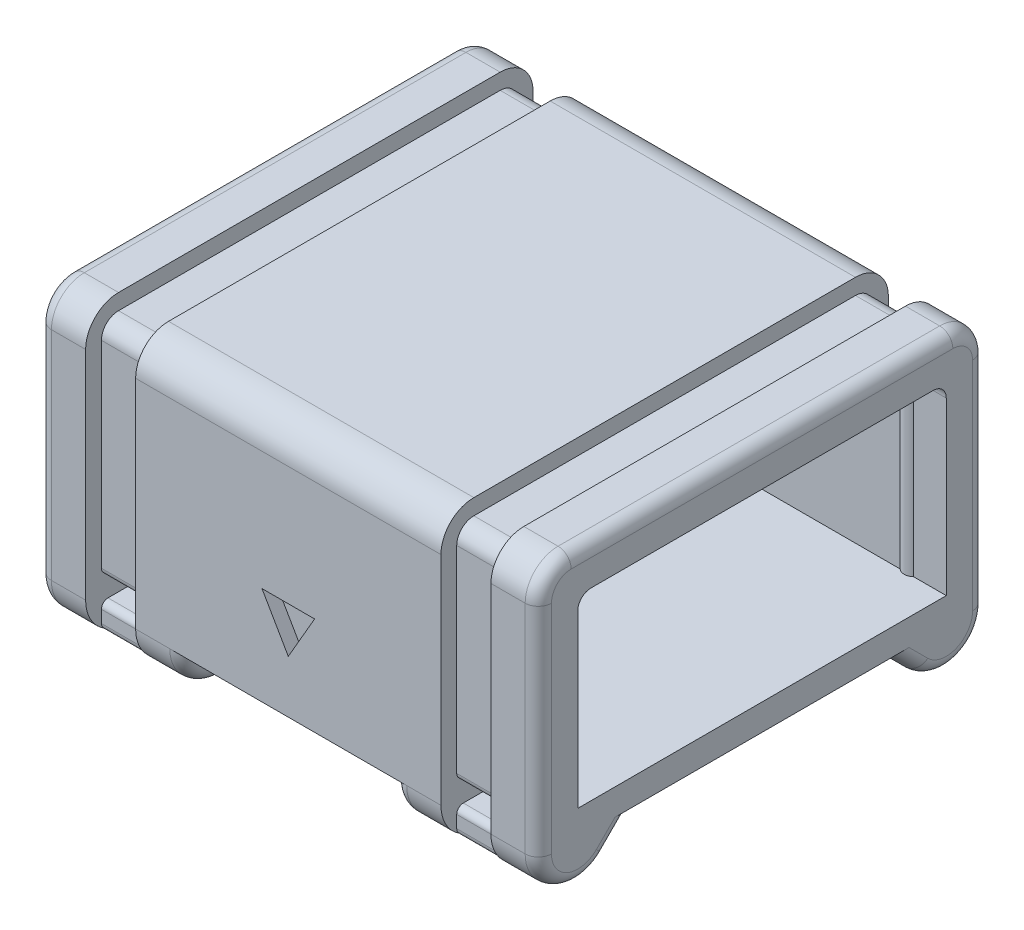
SolidWorks part; units mm, degrees
ref_plane "Ebene vorne" through (0, 0, 0) normal (0, 0, 1) x (1, 0, 0)
ref_plane "Ebene oben" through (0, 0, 0) normal (0, 1, 0) x (1, 0, 0)
ref_plane "Ebene rechts" through (0, 0, 0) normal (1, 0, 0) x (0, 0, -1)
ref_plane "Ebene1" through (13.5, 0, 0) normal (1, 0, 0) x (0, 0, -1)
ref_plane "Ebene2" through (-13.5, 0, 0) normal (1, 0, 0) x (0, 0, -1)
sketch "Skizze2" plane through (0, 0, 0) normal (1, 0, 0) x (0, 0, -1)
  line L0 (-14, 9) -> (14, 9)
  line L4 (-17, 14.5) -> (-17, 0)
  line L5 (14.5, 17) -> (-14.5, 17)
  line L6 (17, 14.5) -> (17, 0)
  line L7 (14, 9) -> (14, 0)
  line L8 (17, 0) -> (14, 0)
  line L9 (-14, 9) -> (-14, 0)
  line L10 (-14, 0) -> (-17, 0)
  line L11 (0, 0) -> (0, 4.6223) construction
  arc A2 (-14.5, 17) -> (-17, 14.5) centre (-14.5, 14.5) ccw
  arc A3 (17, 14.5) -> (14.5, 17) centre (14.5, 14.5) ccw
  dimension "D5" = 3
  dimension "D6" = 34
  dimension "D2" = 2.5
  dimension "D1" = 17
  dimension "D3" = 9
  dimension "D7" = 3
extrude "Aufsatz-Linear austragen2" add sketch "Skizze2" along normal mid plane 38
sketch "Skizze5" plane through (0, 0, -17) normal (0, 0, 1) x (1, 0, 0)
  line L0 (0, 2) -> (-2, 5.4641)
  line L1 (-2, 5.4641) -> (2, 5.4641)
  line L2 (2, 5.4641) -> (0, 2)
  line L3 (0, 5.4641) -> (0, 2) construction
  dimension "D1" = 4
  dimension "D2" = 2
sketch "Skizze9" plane through (0, 0, 17) normal (0, 0, -1) x (-1, 0, 0)
  line L0 (0, 2) -> (-2, 5.4641)
  line L1 (-2, 5.4641) -> (2, 5.4641)
  line L2 (2, 5.4641) -> (0, 2)
  line L3 (0, 5.4641) -> (0, 2) construction
  dimension "D1" = 4
sketch "Skizze8" plane through (0, 0, 0) normal (1, 0, 0) x (0, 0, -1)
  line L0 (14.5, 17) -> (-14.5, 17) construction
  line L17 (-14, 9) -> (14, 9)
  line L18 (14, 9) -> (14, 13)
  line L25 (13, 14) -> (-13, 14)
  line L28 (-14, 13) -> (-14, 9)
  arc A0 (-14, 13) -> (-13, 14) centre (-13, 13) cw
  arc A1 (13, 14) -> (14, 13) centre (13, 13) cw
  dimension "D2" = 1
  dimension "D1" = 3
extrude "Schnitt-Linear austragen3" cut sketch "Skizze8" against normal mid plane 34
sketch "Skizze17" plane through (-19, 0, 0) normal (-1, 0, 0) x (0, 0, 1)
  line L0 (-17, 0) -> (17, 0)
  line L1 (17, 0) -> (17, -2)
  line L2 (11.8787, -4.1213) -> (9.7574, -2)
  line L3 (9.7574, -2) -> (-9.7574, -2)
  line L4 (0, -1.2233) -> (0, -7.3474) construction
  line L5 (-11.8787, -4.1213) -> (-9.7574, -2)
  line L6 (-17, 0) -> (-17, -2)
  line L7 (-14, 0) -> (-17, 0) construction
  arc A0 (17, -2) -> (11.8787, -4.1213) centre (14, -2) cw
  arc A1 (-17, -2) -> (-11.8787, -4.1213) centre (-14, -2) ccw
  point P15 (0, -2)
  point P16 (0, 0)
  dimension "D3" = 3
  dimension "D1" = 2
  dimension "D4" = 90
  dimension "D5" = 5
extrude "Aufsatz-Linear austragen9" add sketch "Skizze17" against normal up to surface (38 mm away) up to face at (19, 8.2036, 0)
sketch "Skizze14" plane through (-19, 0, 0) normal (-1, 0, 0) x (0, 0, 1)
  line L0 (14, 0) -> (14, 9) construction
  line L1 (-14, 9) -> (14, 9)
  line L2 (-14, 9) -> (-14, 0)
  line L3 (-14, 0) -> (14, 0)
  line L4 (14, 9) -> (14, 0)
  line L5 (-14, 9) -> (-14, 0) construction
extrude "Aufsatz-Linear austragen8" add sketch "Skizze14" against normal up to surface (2 mm away) up to face at (-17, 12.069, 0)
sketch "Skizze12" plane through (19, 0, 0) normal (1, 0, 0) x (0, 0, -1)
  line L0 (-14, 9) -> (14, 9) construction
  line L1 (-14, 9) -> (14, 9)
  line L2 (-14, 9) -> (-14, 13)
  line L3 (-13, 14) -> (13, 14)
  line L4 (14, 9) -> (14, 13)
  line L5 (0, 14) -> (0, 5.9274) construction
  line L6 (-14, 0) -> (-14, 9) construction
  line L7 (14, 9) -> (14, 0) construction
  line L8 (-14, 0) -> (-14, 9) construction
  arc A0 (14, 13) -> (13, 14) centre (13, 13) ccw
  arc A1 (-13, 14) -> (-14, 13) centre (-13, 13) ccw
  dimension "D1" = 1
  dimension "D2" = 5
extrude "Schnitt-Linear austragen5" cut sketch "Skizze12" against normal up to surface (2 mm away) up to face at (17, 12.069, 0)
sketch "Skizze19" plane through (0, 14, 0) normal (0, 1, 0) x (1, 0, 0)
  line L0 (15.5, 14) -> (16.5, 14)
  line L3 (0, 0) -> (5.7188, 0) construction
  line L4 (15.5, -14) -> (16.5, -14)
  line L5 (-17, 14) -> (19, 14) construction
  line L6 (19, 14.5) -> (19, -14.5) construction
  arc A0 (15.5, 14) -> (16.5, 14) centre (16, 14.525) ccw
  arc A1 (15.5, -14) -> (16.5, -14) centre (16, -14.525) cw
  dimension "D1" = 1
  dimension "D2" = 2.5
  dimension "D3" = 0.2
extrude "Aufsatz-Linear austragen10" add sketch "Skizze19" against normal blind 14
sketch "Skizze20" plane through (-17, 0, 0) normal (1, 0, 0) x (0, 0, -1)
  circle A0 centre (0, 2) radius 1.5
extrude "Schnitt-Linear austragen7" cut sketch "Skizze20" against normal through all and the other way through all contours A0
pattern_linear "Lineares Muster1" count 2 spacing 24 along (-1, 0, 0) of "Aufsatz-Linear austragen10"
sketch "Skizze21" plane through (0, 0, 0) normal (0, 0, 1) x (1, 0, 0)
  line L0 (-8, -2) -> (8, -2)
  line L1 (8, -2) -> (8, -5)
  line L2 (8, -5) -> (-8, -5)
  line L3 (-8, -5) -> (-8, -2)
  line L4 (19, -2) -> (-19, -2) construction
  line L5 (0, 0) -> (0, -2) construction
  dimension "D1" = 16
  dimension "D2" = 3
extrude "Schnitt-Linear austragen9" cut sketch "Skizze21" against normal through all both and the other way through all
sketch "Skizze10" plane through (-19, -2, 0) normal (1, 0, 0) x (0, -1, 0)
  line L0 (-1.8688, 0) -> (-7, 0) construction
  line L1 (-7, -6.2274) -> (-7, 6.2274) construction
  line L3 (-17, -0.75) -> (-17, 0.75)
  line L4 (-17, -0.75) -> (-7, -0.75)
  line L5 (-7, -0.75) -> (-7, 0.75)
  line L6 (-17, 0.75) -> (-7, 0.75)
  line L7 (-14, -10.65) -> (-14, -9.15)
  line L8 (-14, -10.65) -> (-7, -10.65)
  line L9 (-7, -10.65) -> (-7, -9.15)
  line L10 (-14, -9.15) -> (-7, -9.15)
  line L11 (-14, -7.35) -> (-14, -5.85)
  line L12 (-14, -7.35) -> (-7, -7.35)
  line L13 (-7, -7.35) -> (-7, -5.85)
  line L14 (-14, -5.85) -> (-7, -5.85)
  line L15 (-14, -4.05) -> (-14, -2.55)
  line L16 (-14, -4.05) -> (-7, -4.05)
  line L17 (-7, -4.05) -> (-7, -2.55)
  line L18 (-14, -2.55) -> (-7, -2.55)
  line L19 (-14, 2.55) -> (-14, 4.05)
  line L20 (-14, 2.55) -> (-7, 2.55)
  line L21 (-7, 2.55) -> (-7, 4.05)
  line L22 (-14, 4.05) -> (-7, 4.05)
  line L23 (-14, 5.85) -> (-14, 7.35)
  line L24 (-14, 5.85) -> (-7, 5.85)
  line L25 (-7, 5.85) -> (-7, 7.35)
  line L26 (-14, 7.35) -> (-7, 7.35)
  line L27 (-17, 9.15) -> (-17, 10.65)
  line L28 (-17, 9.15) -> (-7, 9.15)
  line L29 (-7, 9.15) -> (-7, 10.65)
  line L30 (-17, 10.65) -> (-7, 10.65)
  point P5 (-7, 0)
  dimension "D1" = 7
  dimension "D3" = 1.5
  dimension "D4" = 1.8
  dimension "D5" = 1.8
  dimension "D6" = 1.8
  dimension "D7" = 5
  dimension "D8" = 10
extrude "Schnitt-Linear austragen8" cut sketch "Skizze10" along normal blind 1
extrude "Schnitt-Linear austragen10" cut sketch "Skizze5" along normal blind 1
extrude "Schnitt-Linear austragen11" cut sketch "Skizze9" along normal blind 1
fillet "Verrundung1" radius 1 18 edges at (-19, 6.25, -17) (19, 6.25, -17) (-19, 16.2678, -16.2678) (19, 16.2678, -16.2678) (-19, 17, 0) (19, 17, 0) (-19, 6.25, 17) (19, 6.25, 17) (19, 16.2678, 16.2678) (-19, 16.2678, 16.2678) (-19, -3.0607, -10.818) (19, -3.0607, -10.818) (19, -4.7716, -15.1481) (-19, -4.7716, -15.1481) (-19, -3.0607, 10.818) (19, -3.0607, 10.818) (19, -4.7716, 15.1481) (-19, -4.7716, 15.1481)
fillet "Verrundung4" radius 1 8 edges at (8, -3.0607, 10.818) (8, -4.7716, 15.1481) (-8, -3.0607, 10.818) (-8, -4.7716, 15.1481) (8, -4.7716, -15.1481) (8, -3.0607, -10.818) (-8, -4.7716, -15.1481) (-8, -3.0607, -10.818)
sketch "Skizze24" plane through (13.5, 0, 0) normal (1, 0, 0) x (0, 0, -1)
  line L0 (-17, -2) -> (-17, 14.5) construction
  line L1 (17, 14.5) -> (17, -2) construction
  line L2 (-14.5, 17) -> (14.5, 17) construction
  line L3 (17, 14.5) -> (17, -5)
  line L4 (-14.5, 17) -> (14.5, 17)
  line L5 (-17, -5) -> (-17, 14.5)
  arc A0 (-14.5, 17) -> (-17, 14.5) centre (-14.5, 14.5) ccw construction
  arc A1 (17, 14.5) -> (14.5, 17) centre (14.5, 14.5) ccw construction
  arc A2 (17, 14.5) -> (14.5, 17) centre (14.5, 14.5) ccw
  arc A3 (-14.5, 17) -> (-17, 14.5) centre (-14.5, 14.5) ccw
  dimension "D1" = 22
extrude "Schnitt-Linear-Austragen-Dünn1" cut sketch "Skizze24" against normal blind 1.9 and the other way blind 1.9 thin
sketch "Skizze25" plane through (-13.5, 0, 0) normal (1, 0, 0) x (0, 0, -1)
  line L0 (-17, -5) -> (-17, 14.5) construction
  line L1 (-14.5, 17) -> (14.5, 17) construction
  line L2 (17, 14.5) -> (17, -5) construction
  line L3 (-17, -5) -> (-17, 14.5)
  line L4 (-14.5, 17) -> (14.5, 17)
  line L5 (17, 14.5) -> (17, -5)
  arc A0 (-14.5, 17) -> (-17, 14.5) centre (-14.5, 14.5) ccw construction
  arc A1 (17, 14.5) -> (14.5, 17) centre (14.5, 14.5) ccw construction
  arc A2 (-14.5, 17) -> (-17, 14.5) centre (-14.5, 14.5) ccw
  arc A3 (17, 14.5) -> (14.5, 17) centre (14.5, 14.5) ccw
extrude "Schnitt-Linear-Austragen-Dünn2" cut sketch "Skizze25" against normal blind 1.9 and the other way blind 1.9 thin
sketch "Skizze26" plane through (-17, 0, 0) normal (1, 0, 0) x (0, 0, -1)
  line L0 (-14, 13) -> (-14, 0) construction
  line L1 (-14, 5.7) -> (-12, 5.7)
  line L2 (-14, 5.7) -> (-14, 14)
  line L3 (-14, 14) -> (-12, 14)
  line L4 (-12, 5.7) -> (-12, 14)
  line L5 (13, 14) -> (-13, 14) construction
  line L6 (-14, 0) -> (14, 0) construction
  line L7 (0, 9.4882) -> (0, 15.0049) construction
  line L8 (12, 5.7) -> (12, 14)
  line L9 (14, 14) -> (12, 14)
  line L10 (14, 5.7) -> (14, 14)
  line L11 (14, 5.7) -> (12, 5.7)
  dimension "D1" = 2
  dimension "D2" = 5.7
extrude "Aufsatz-Linear austragen11" add sketch "Skizze26" along normal blind 2
sketch "Skizze27" plane through (0, 0, 0) normal (0, 0, 1) x (1, 0, 0)
  line L0 (0, -7.7907) -> (0, -15.1982) construction
  line L1 (15.4, -1) -> (11.6, -1)
  line L2 (15.4, -1) -> (15.4, -2.7)
  line L3 (15.4, -2.7) -> (11.6, -2.7)
  line L4 (11.6, -1) -> (11.6, -2.7)
  line L5 (-11.6, -1) -> (-11.6, -2.7)
  line L6 (-15.4, -2.7) -> (-11.6, -2.7)
  line L7 (-15.4, -1) -> (-15.4, -2.7)
  line L8 (-15.4, -1) -> (-11.6, -1)
  line L9 (11.6, 14.5) -> (11.6, -4.4) construction
  line L10 (15.4, 14.5) -> (15.4, -4.4) construction
  line L11 (18.7, 0) -> (-18.7, 0) construction
  point P11 (11.9536, -2.5129)
  point P14 (0, 0)
  dimension "D1" = 1.7
  dimension "D2" = 1
extrude "Schnitt-Linear austragen13" cut sketch "Skizze27" against normal through all both and the other way through all
fillet "Verrundung5" radius 0.5 16 edges at (13.5, -2.7, 15.8) (13.5, -1, 15.8) (13.5, -2.7, -10.4574) (13.5, -2.7, 10.4574) (13.5, -2.7, -15.8) (13.5, -1, -15.8) (-13.5, -1, -15.8) (-13.5, -2.7, -15.8) (-13.5, -2.7, 10.4574) (-13.5, -2.7, -10.4574) (-13.5, -2.7, 15.8) (-13.5, -1, 15.8) (-13.5, -4.4, 15.8) (13.5, -4.4, 15.8) (-13.5, -4.4, -15.8) (13.5, -4.4, -15.8)
sketch "Skizze28" plane through (-19, 0, 0) normal (-1, 0, 0) x (0, 0, 1)
  line L0 (10.5, 0.5) -> (14, 0.5) construction
  line L1 (0, -12.1) -> (0, 12.1) construction
  line L2 (18.7, 0) -> (-18.7, 0) construction
  text T0 "R" font "Arial" height in points 14
  point P4 (7.1637, 0)
  point P5 (12.9613, 0)
  point P8 (7.8582, 0)
  dimension "D1" = 14
  dimension "D2" = 0.5
  dimension "D3" = 3.5
extrude "Schnitt-Linear austragen14" cut sketch "Skizze28" against normal blind 1
